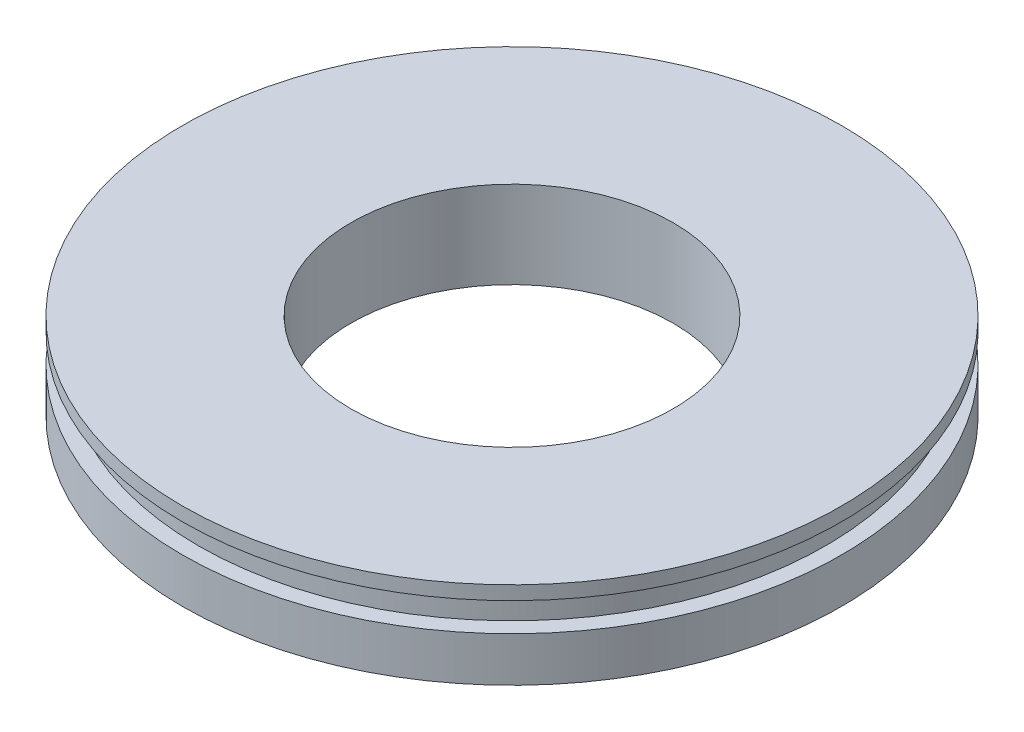
SolidWorks part; units mm, degrees
material "6061-T6 (SS)"
ref_plane "X-Y Datum" through (0, 0, 0) normal (0, 0, 1) x (1, 0, 0)
ref_plane "X-Z Datum" through (0, 0, 0) normal (0, 1, 0) x (1, 0, 0)
ref_plane "Y-Z Datum" through (0, 0, 0) normal (1, 0, 0) x (0, 0, -1)
sketch "Sketch1" plane through (0, 0, 0) normal (1, 0, 0) x (0, 0, -1)
  line L0 (-14.2875, 2.6941) -> (-14.2875, -5.0208)
  line L1 (-14.2875, -5.0208) -> (-29.21, -5.0208)
  line L3 (-29.21, -1.0621) -> (-27.8041, -1.0621)
  line L4 (-27.8041, -1.0621) -> (-27.8041, 1.4779)
  line L5 (-27.8041, 1.4779) -> (-29.21, 1.4779)
  line L6 (-29.21, 1.4779) -> (-29.21, 2.6941)
  line L7 (-29.21, 2.6941) -> (-14.2875, 2.6941)
  line L8 (0, 0) -> (0, -47872.0541) construction
  line L9 (0, 0) -> (-47872.0541, 0) construction
  line L10 (-29.21, -1.0621) -> (-29.21, -5.0208)
  line L11 (-14.7421, 2.6941) -> (15.0495, 2.6941) construction
  line L12 (-29.3688, 12.7) -> (-29.3687, -12.7) construction
  line L13 (14.2875, -5.0208) -> (-14.2875, -5.0208) construction
  line L14 (-29.3687, -1.0621) -> (29.3687, -1.0621) construction
  circle A0 centre (-28.6931, 0.2079) radius 0.889 construction
  point P15 (-29.3687, 0)
  point P16 (-27.8041, 0.2079)
  dimension "D3" = 1.778
  dimension "D1" = 28.575
  dimension "D2" = 58.42
  dimension "D4" = 2.54
  dimension "D5" = 25.4
  dimension "D6" = 58.7375
  dimension "D7" = 1.5646
revolve "Revolve1" add sketch "Sketch1" angle 360 about L8
